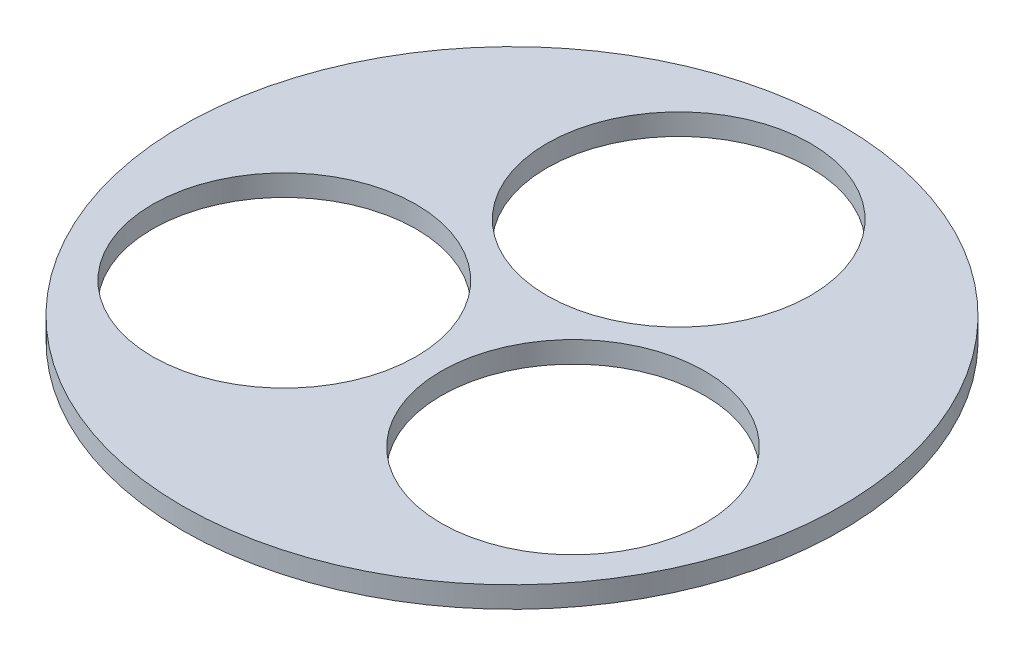
SolidWorks part; units mm, degrees
ref_plane "Front Plane" through (0, 0, 0) normal (0, 0, 1) x (1, 0, 0)
ref_plane "Top Plane" through (0, 0, 0) normal (0, 1, 0) x (1, 0, 0)
ref_plane "Right Plane" through (0, 0, 0) normal (1, 0, 0) x (0, 0, -1)
sketch "Sketch1" plane through (0, 0, 0) normal (0, 1, 0) x (1, 0, 0)
  line L0 (0, 0) -> (0, 49.784) construction
  circle A0 centre (0, 0) radius 98.425
  circle A1 centre (0, 49.784) radius 39.37
  circle A2 centre (43.1142, -24.892) radius 39.37
  circle A3 centre (-43.1142, -24.892) radius 39.37
  point P12 (0, 0)
  dimension "D1" = 78.74
  dimension "D3" = 196.85
  dimension "D4" = 49.784
  dimension "D2" = 3
extrude "Boss-Extrude1" add sketch "Sketch1" along normal blind 6.35
